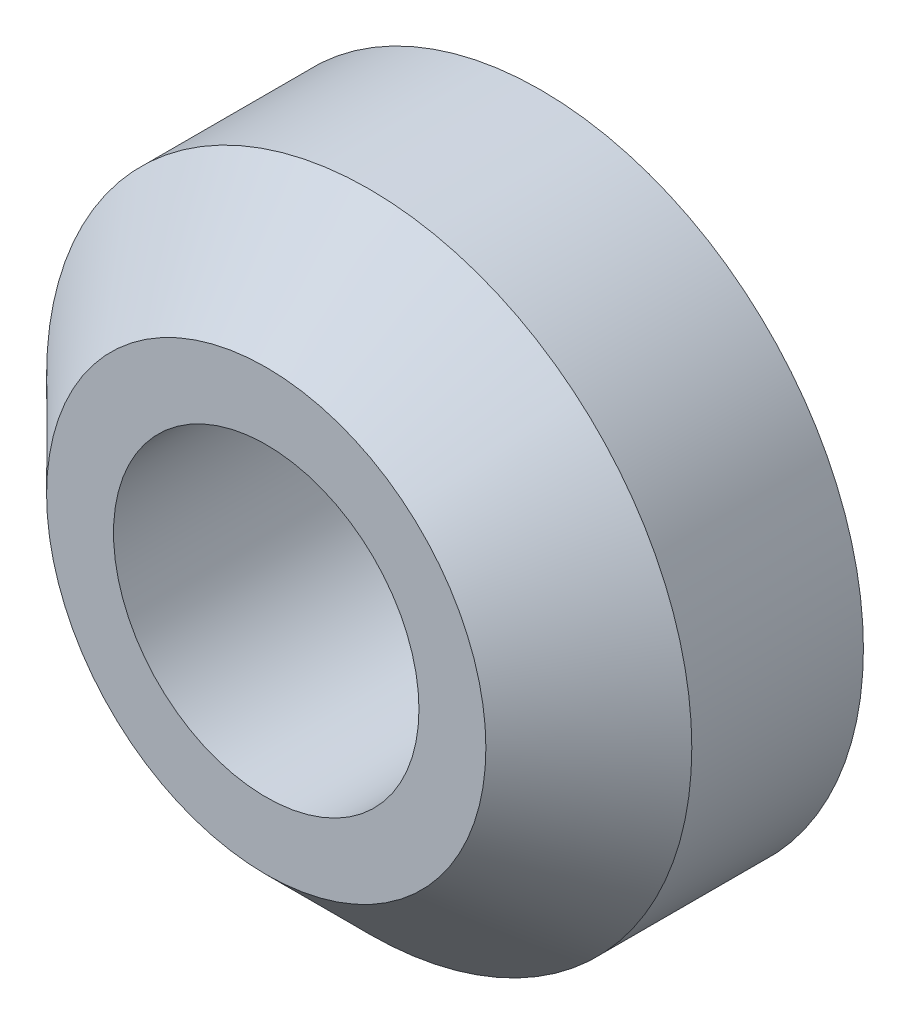
SolidWorks part; units mm, degrees
ref_plane "Front Plane" through (0, 0, 0) normal (0, 0, 1) x (1, 0, 0)
ref_plane "Top Plane" through (0, 0, 0) normal (0, 1, 0) x (1, 0, 0)
ref_plane "Right Plane" through (0, 0, 0) normal (1, 0, 0) x (0, 0, -1)
sketch "Sketch1" plane through (0, 0, 0) normal (0, 0, 1) x (1, 0, 0)
  circle A0 centre (0, 0) radius 2.3876
  circle A1 centre (0, 0) radius 1.1303
extrude "Extrude1" add sketch "Sketch1" along normal blind 2.032
chamfer "Chamfer1" distance 0.762 angle 45 1 edges at (2.3876, 0, 2.032)
